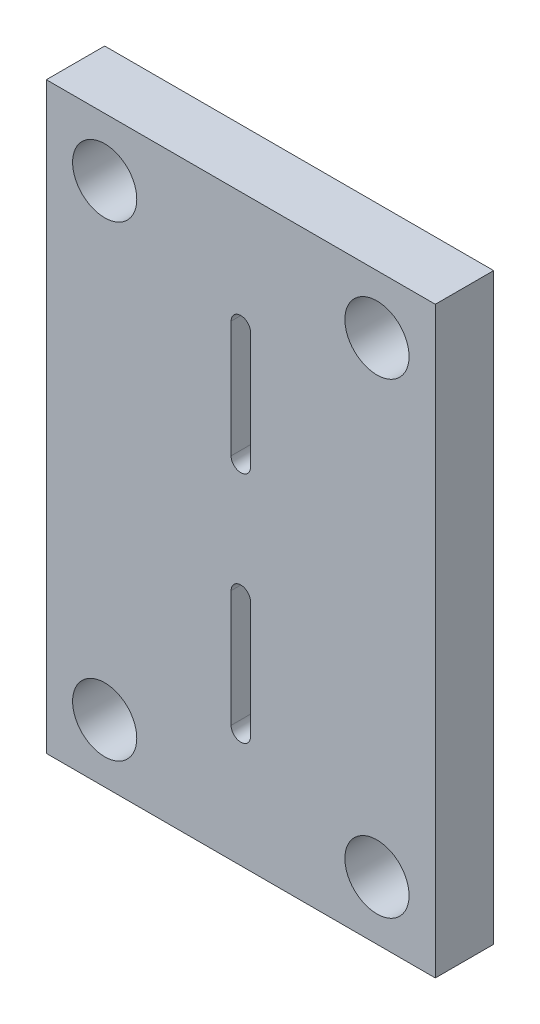
SolidWorks part; units mm, degrees
material "Acrílico (Impacto medio-alto)"
ref_plane "Alzado" through (0, 0, 0) normal (0, 0, 1) x (1, 0, 0)
ref_plane "Planta" through (0, 0, 0) normal (0, 1, 0) x (1, 0, 0)
ref_plane "Vista lateral" through (0, 0, 0) normal (1, 0, 0) x (0, 0, -1)
sketch "Croquis1" plane through (0, 0, 0) normal (0, 0, 1) x (1, 0, 0)
  line L1 (10, -15) -> (-10, -15)
  line L2 (10, -15) -> (10, 15)
  line L3 (10, 15) -> (-10, 15)
  line L4 (-10, -15) -> (-10, 15)
  line L5 (10, -15) -> (-10, 15) construction
  line L6 (10, 15) -> (-10, -15) construction
  circle A0 centre (-7, 12) radius 1.65
  circle A1 centre (7, 12) radius 1.65
  circle A2 centre (7, -12) radius 1.65
  circle A3 centre (-7, -12) radius 1.65
  point P0 (0, 0)
  dimension "D1" = 3.3
  dimension "D4" = 3
  dimension "D5" = 3
  dimension "D6" = 3
  dimension "D7" = 3
  dimension "D8" = 3
  dimension "D2" = 30
  dimension "D3" = 20
extrude "Saliente-Extruir1" add sketch "Croquis1" along normal blind 3
sketch "Croquis2" plane through (0, 0, 3) normal (0, 0, 1) x (1, 0, 0)
  line L0 (0, -9) -> (0, -3) construction
  line L1 (-0.5, -9) -> (-0.5, -3)
  line L2 (0.5, -9) -> (0.5, -3)
  line L3 (0, 3) -> (0, 9) construction
  line L4 (-0.5, 3) -> (-0.5, 9)
  line L5 (0.5, 3) -> (0.5, 9)
  arc A0 (-0.5, -9) -> (0.5, -9) centre (0, -9) ccw
  arc A1 (0.5, -3) -> (-0.5, -3) centre (0, -3) ccw
  arc A2 (-0.5, 3) -> (0.5, 3) centre (0, 3) ccw
  arc A3 (0.5, 9) -> (-0.5, 9) centre (0, 9) ccw
  point P3 (0, -6)
  point P8 (0, 6)
  point P15 (0.5, -8.972)
  point P17 (0, 0)
  dimension "D2" = 3
  dimension "D4" = 0.5
  dimension "D1" = 6
  dimension "D3" = 6
extrude "Cortar-Extruir1" cut sketch "Croquis2" against normal up to next
